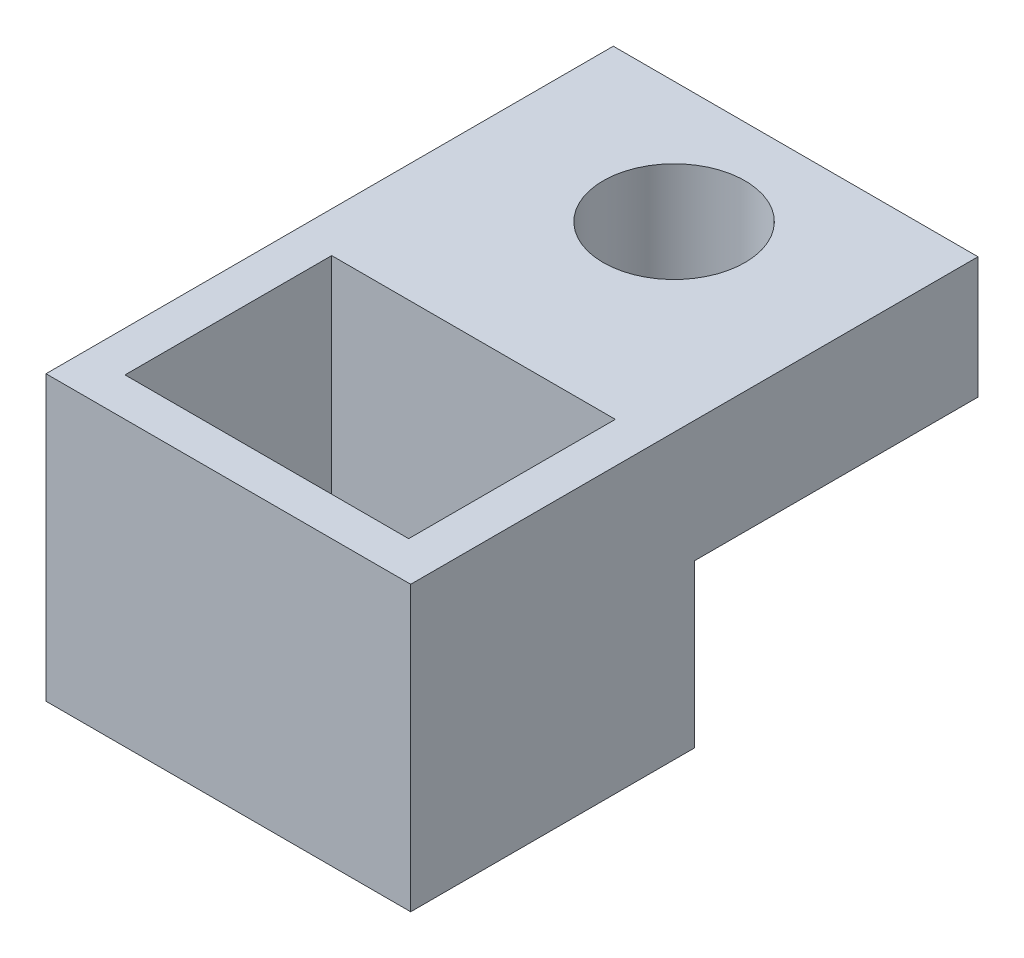
SolidWorks part; units mm, degrees
ref_plane "Front Plane" through (0, 0, 0) normal (0, 0, 1) x (1, 0, 0)
ref_plane "Top Plane" through (0, 0, 0) normal (0, 1, 0) x (1, 0, 0)
ref_plane "Right Plane" through (0, 0, 0) normal (1, 0, 0) x (0, 0, -1)
sketch "Sketch4" plane through (0, 0, 0) normal (1, 0, 0) x (0, 0, -1)
  line L0 (0, 0) -> (0, -4)
  line L1 (0, -4) -> (-7, -4)
  line L2 (-7, -4) -> (-7, 3)
  line L3 (-7, 3) -> (7, 3)
  line L4 (7, 3) -> (7, 0)
  line L5 (7, 0) -> (0, 0)
  dimension "D1" = 4
  dimension "D2" = 3
  dimension "D3" = 7
  dimension "D4" = 7
extrude "Boss-Extrude2" add sketch "Sketch4" along normal blind 9
sketch "Sketch6" plane through (0, 3, 0) normal (0, 1, 0) x (1, 0, 0)
  line L0 (4.5, 7) -> (4.5, -7) construction
  line L1 (9, 7) -> (0, 7) construction
  line L2 (9, -7) -> (0, -7) construction
  line L4 (1, -0.95) -> (8, -0.95)
  line L5 (1, -0.95) -> (1, -6.05)
  line L6 (1, -6.05) -> (8, -6.05)
  line L7 (8, -0.95) -> (8, -6.05)
  circle A0 centre (4.5, 4) radius 1.75
  point P12 (8, -3.5)
  dimension "D1" = 3.5
  dimension "D2" = 3.5
  dimension "D3" = 5.1
  dimension "D4" = 3.5
  dimension "D5" = 3.5
  dimension "D6" = 3
extrude "Cut-Extrude1" cut sketch "Sketch6" against normal through all
equation "\"D4@Sketch6\"=\"D2@Sketch6\""
